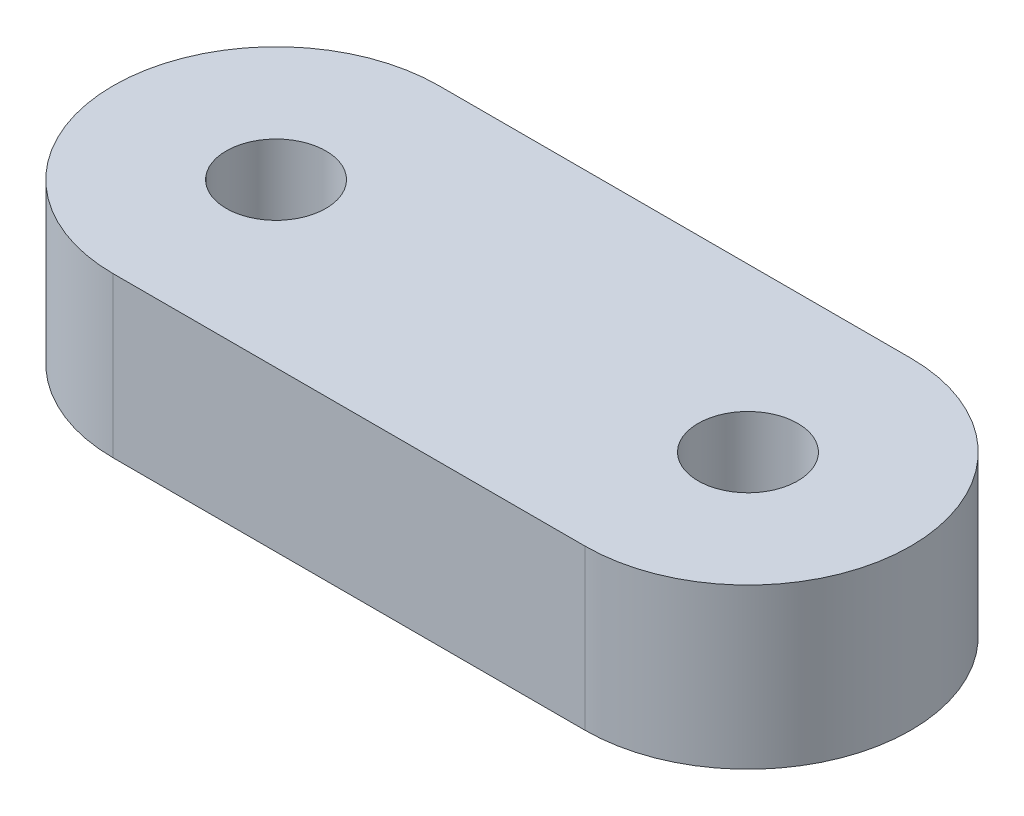
SolidWorks part; units mm, degrees
ref_plane "Front Plane" through (0, 0, 0) normal (0, 0, 1) x (1, 0, 0)
ref_plane "Top Plane" through (0, 0, 0) normal (0, 1, 0) x (1, 0, 0)
ref_plane "Right Plane" through (0, 0, 0) normal (1, 0, 0) x (0, 0, -1)
sketch "Sketch1" plane through (0, 0, 0) normal (0, 1, 0) x (1, 0, 0)
  line L0 (12, 0) -> (12, 15.5804) construction
  line L1 (-7.1, 4.9) -> (7.1, 4.9)
  line L2 (-12, 0) -> (-12, 15.5804) construction
  line L3 (-7.1, -4.9) -> (7.1, -4.9)
  line L4 (-7.1, 4.9) -> (-7.1, -4.9) construction
  line L5 (-7.1, 4.9) -> (7.1, -4.9) construction
  line L6 (-7.1, -4.9) -> (7.1, 4.9) construction
  line L7 (7.1, 4.9) -> (7.1, -4.9) construction
  line L8 (0, 4.9) -> (0, -4.9) construction
  arc A0 (-7.1, 4.9) -> (-7.1, -4.9) centre (-7.1, 0) ccw
  arc A1 (7.1, -4.9) -> (7.1, 4.9) centre (7.1, 0) ccw
  circle A2 centre (-7.1, 0) radius 1.5
  circle A3 centre (7.1, 0) radius 1.5
  point P0 (0, 0)
  dimension "D2" = 14.2
  dimension "D4" = 4.9
  dimension "D5" = 3
  dimension "D1" = 9.8
extrude "Boss-Extrude1" add sketch "Sketch1" along normal blind 4.8
